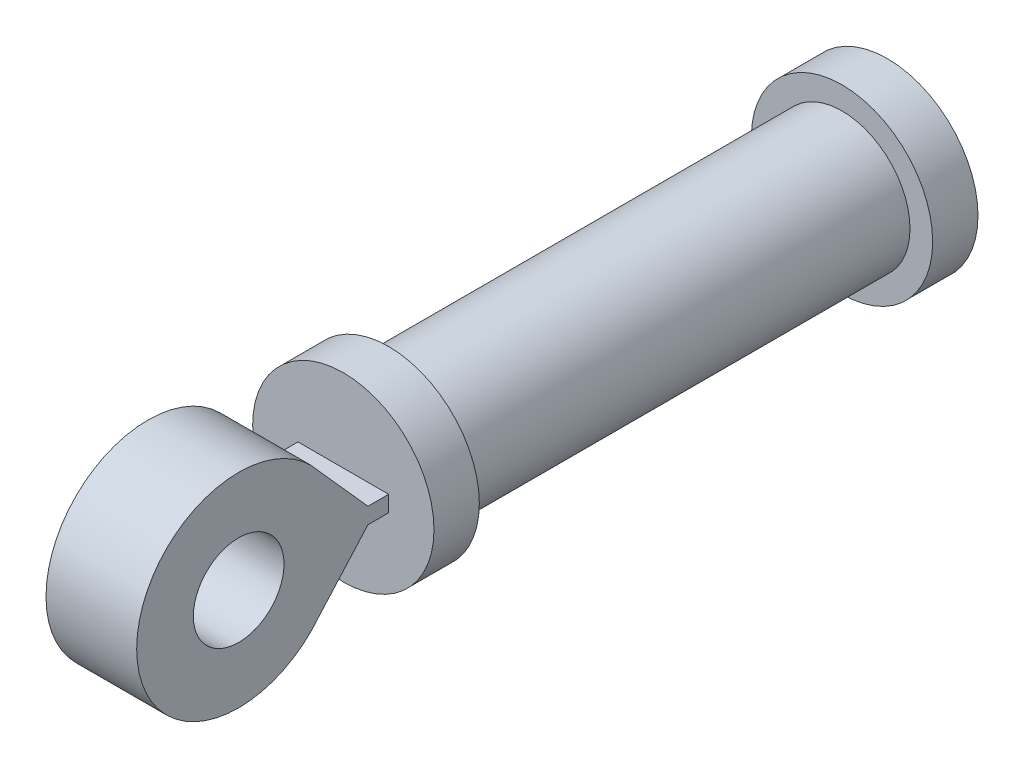
SolidWorks part; units mm, degrees
ref_plane "Front Plane" through (0, 0, 0) normal (0, 0, 1) x (1, 0, 0)
ref_plane "Top Plane" through (0, 0, 0) normal (0, 1, 0) x (1, 0, 0)
ref_plane "Right Plane" through (0, 0, 0) normal (1, 0, 0) x (0, 0, -1)
sketch "Sketch3" plane through (0, 0, 0) normal (0, 0, 1) x (1, 0, 0)
  circle A0 centre (0, 0) radius 10
extrude "Boss-Extrude3" add sketch "Sketch3" along normal blind 5
hole_wizard "CBORE for M4 Cheese Head Screw1" positions "Sketch15" profile "Sketch14" counterbore size "M4" standard "AS"
sketch "Sketch15" plane through (0, 0, 5) normal (0, 0, 1) x (1, 0, 0)
  point P0 (0, 0)
sketch "Sketch14" plane through (0, 0, 5) normal (1, 0, 0) x (0, -1, 0)
  line L0 (0, 0) -> (0, 8.9421)
  line L1 (0, 8.9421) -> (2.4, 7.5)
  line L2 (2.4, 7.5) -> (2.4, 2.6)
  line L3 (2.4, 2.6) -> (4, 2.6)
  line L5 (4, 2.6) -> (4, 0.025)
  line L6 (4, 0.025) -> (4.025, 0)
  line L7 (4.025, 0) -> (0, 0)
  line L8 (-4, 0.025) -> (-4.025, 0) construction
  line L10 (0, 8.9421) -> (-2.4, 7.5) construction
  line L11 (0, -6.35) -> (0, 107.95) construction
  dimension "Hole Dia." = 4.8
  dimension "Hole Depth" = 7.5
  dimension "C'Bore Dia." = 8
  dimension "C'Bore Depth" = 2.6
  dimension "Near C'Sink Dia." = 8.05
  dimension "Near C'Sink Angle" = 90
  dimension "Drill Angle" = 118
sketch "Sketch16" plane through (0, 0, 5) normal (0, 0, 1) x (1, 0, 0)
  circle A0 centre (0, 0) radius 7.5
extrude "Boss-Extrude7" add sketch "Sketch16" along normal blind 50
sketch "Sketch19" plane through (0, 0, 55) normal (0, 0, 1) x (1, 0, 0)
  circle A0 centre (0, 0) radius 4
extrude "Cut-Extrude3" cut sketch "Sketch19" against normal blind 50
sketch "Sketch20" plane through (0, 0, 55) normal (0, 0, 1) x (1, 0, 0)
  circle A0 centre (0, 0) radius 10
extrude "Boss-Extrude8" add sketch "Sketch20" along normal blind 5
sketch "Sketch21" plane through (0, 0, 60) normal (0, 0, 1) x (1, 0, 0)
  line L1 (-51.5692, -38.0567) -> (51.5692, -38.0567)
  line L2 (-51.5692, -38.0567) -> (-51.5692, 38.0567)
  line L3 (-51.5692, 38.0567) -> (51.5692, 38.0567)
  line L4 (51.5692, -38.0567) -> (51.5692, 38.0567)
  line L5 (-51.5692, -38.0567) -> (51.5692, 38.0567) construction
  line L6 (-51.5692, 38.0567) -> (51.5692, -38.0567) construction
  point P0 (0, 0)
extrude "Boss-Extrude9" add sketch "Sketch21" along normal blind 70
scale "Scale1" scale about centroid uniform scaling yes scale factor 2
sketch "Sketch31" plane through (103.1384, 0, 0) normal (1, 0, 0) x (0, 0, -1)
  line L0 (-26.0722, 1.7667) -> (-26.0722, 93.7773)
  line L1 (-26.0722, -20) -> (-26.0722, 20) construction
  line L2 (-26.0722, 1.7667) -> (-30.6339, 1.7667)
  line L3 (-26.0722, -1.7667) -> (-30.6339, -1.7667)
  line L4 (-26.0722, -1.7667) -> (-26.0722, 0)
  line L5 (-26.0722, 0) -> (-26.0722, 1.7667)
  line L6 (-30.6339, 1.7667) -> (-41.415, 13.8371)
  line L7 (-30.6339, -1.7667) -> (-41.415, -13.8371)
  line L8 (-26.0722, 93.7773) -> (-178.9269, 93.7773)
  line L9 (-178.9269, 93.7773) -> (-178.9269, -90.3815)
  line L10 (-178.9269, -90.3815) -> (-26.0722, -90.3815)
  line L11 (-26.0722, -90.3815) -> (-26.0722, -1.7667)
  arc A0 (-41.415, 13.8371) -> (-41.415, -13.8371) centre (-59.1572, 0) ccw
  circle A1 centre (-59.1572, 0) radius 10
  line M4 (-26.0722, -76.1134) -> (-26.0722, 76.1134)
  line M5 (-26.0722, 76.1134) -> (-166.0722, 76.1134)
  line M6 (-166.0722, 76.1134) -> (-166.0722, -76.1134)
  line M7 (-166.0722, -76.1134) -> (-26.0722, -76.1134)
extrude "Cut-Extrude11" cut sketch "Sketch31" against normal through all contours A0 L6 L2 L3 L7 M4 M5 M6 M7 | L10 L11 L0 L8 L9 M7 M6 M5 | A1
sketch "Sketch32" plane through (0, 1.7667, 0) normal (0, 1, 0) x (1, 0, 0)
  line L0 (0, -26.0722) -> (0, -33.8872) construction
  line L1 (-19.9218, -26.0722) -> (19.9218, -26.0722) construction
  line L2 (-10, -26.0722) -> (0, -26.0722) construction
  line L3 (-19.9218, -26.0722) -> (19.9218, -26.0722) construction
  line L4 (0, -26.0722) -> (10, -26.0722) construction
  line L5 (-10, -26.0722) -> (-10, -81.6572)
  line L6 (-103.1384, -81.6572) -> (103.1384, -81.6572) construction
  line L7 (-10, -81.6572) -> (-103.1384, -81.6572)
  line L8 (-103.1384, -81.6572) -> (-103.1384, -26.0722)
  line L9 (-103.1384, -26.0722) -> (-10, -26.0722)
  line L10 (10, -26.0722) -> (103.1384, -26.0722)
  line L11 (103.1384, -26.0722) -> (103.1384, -81.6572)
  line L12 (103.1384, -81.6572) -> (10, -81.6572)
  line L13 (10, -81.6572) -> (10, -26.0722)
extrude "Cut-Extrude12" cut sketch "Sketch32" against normal mid plane 80
